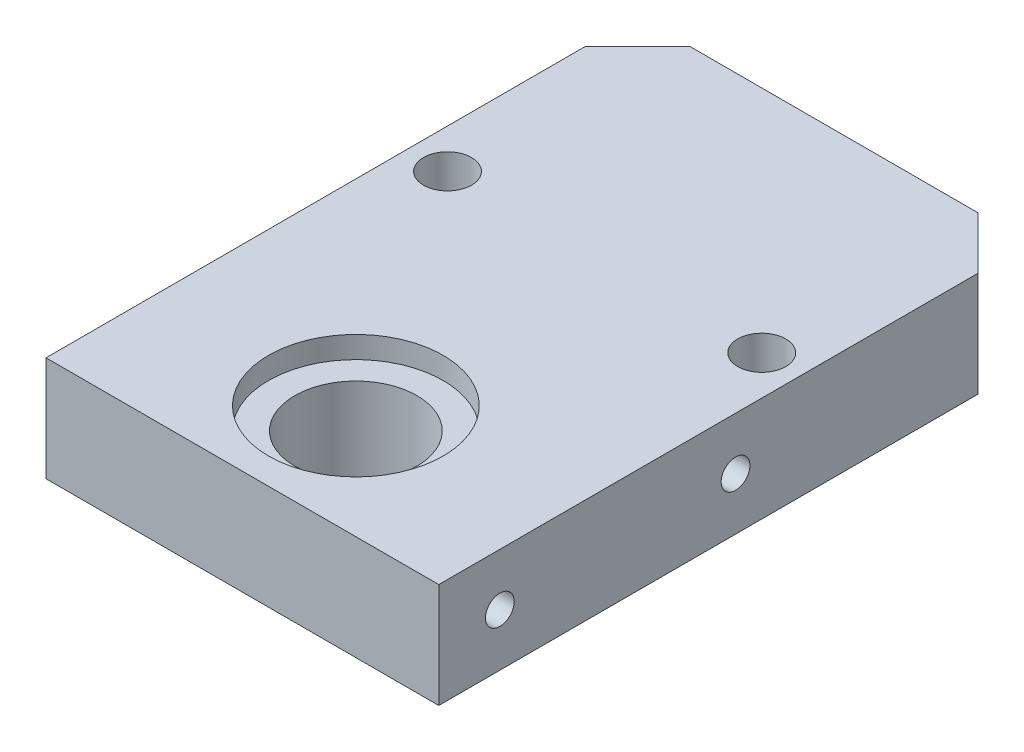
SolidWorks part; units mm, degrees
ref_plane "Front Plane" through (0, 0, 0) normal (0, 0, 1) x (1, 0, 0)
ref_plane "Top Plane" through (0, 0, 0) normal (0, 1, 0) x (1, 0, 0)
ref_plane "Right Plane" through (0, 0, 0) normal (1, 0, 0) x (0, 0, -1)
sketch "Sketch1" plane through (0, 0, 0) normal (0, 1, 0) x (1, 0, 0)
  line L0 (-16.5, 33.8889) -> (-22.5, 27.8889)
  line L1 (-22.5, -33.8889) -> (22.5, -33.8889)
  line L2 (-22.5, -33.8889) -> (-22.5, 27.8889)
  line L3 (-16.5, 33.8889) -> (16.5, 33.8889)
  line L4 (22.5, -33.8889) -> (22.5, 27.8889)
  line L5 (-22.5, -33.8889) -> (22.5, 33.8889) construction
  line L6 (-22.5, 33.8889) -> (22.5, -33.8889) construction
  line L7 (16.5, 33.8889) -> (22.5, 27.8889)
  circle A0 centre (-18, 7.6111) radius 2.75
  circle A1 centre (18, 7.6111) radius 2.75
  circle A2 centre (0, -20.8889) radius 7
  point P0 (0, 0)
  dimension "D8" = 18
  dimension "D10" = 41.5
  dimension "D11" = 41.5
  dimension "D12" = 13
  dimension "D1" = 45
  dimension "D2" = 67.7778
  dimension "D3" = 45
  dimension "D4" = 6
  dimension "D5" = 6
  dimension "D6" = 45
  dimension "D7" = 6
  dimension "D9" = 18
  dimension "D13" = 22.5
extrude "Boss-Extrude1" add sketch "Sketch1" along normal blind 12
hole_wizard "M4 Tapped Hole1" positions "Sketch2" profile "Sketch3" tap size "M4" standard "DIN"
sketch "Sketch2" plane through (-22.5, 0, 0) normal (-1, 0, 0) x (0, 0, 1)
  line L1 (-27.8889, 12) -> (33.8889, 12) construction
  line L2 (33.8889, 12) -> (33.8889, 0) construction
  point P0 (-0.1111, 6)
  point P2 (26.8889, 6)
  dimension "D1" = 6
  dimension "D2" = 6
  dimension "D3" = 7
  dimension "D4" = 34
sketch "Sketch3" plane through (-22.5, 6, -0.1111) normal (0, 1, 0) x (0, 0, 1)
  line L0 (0, 0) -> (0, 14.9914)
  line L1 (0, 14.9914) -> (1.65, 14)
  line L2 (1.65, 14) -> (1.65, 0)
  line L5 (1.65, 0) -> (0, 0)
  line L10 (0, 14.9914) -> (-1.65, 14) construction
  line L11 (0, -6.35) -> (0, 107.95) construction
  dimension "Tap Drill Dia." = 3.3
  dimension "Tap Drill Depth" = 14
  dimension "Drill Angle" = 118
cosmetic thread "Hole Thread1" parameters "D1"=10, "D2"=4
cosmetic thread "Hole Thread2" parameters "D1"=10, "D2"=4
hole_wizard "M4 Tapped Hole2" positions "Sketch4" profile "Sketch5" tap size "M4" standard "DIN"
sketch "Sketch4" plane through (22.5, 0, 0) normal (1, 0, 0) x (0, 0, -1)
  line L0 (-33.8889, 0) -> (27.8889, 0) construction
  line L1 (-33.8889, 12) -> (-33.8889, 0) construction
  point P0 (-26.8889, 6)
  point P2 (0.1111, 6)
  dimension "D1" = 6
  dimension "D2" = 6
  dimension "D3" = 7
  dimension "D4" = 27
sketch "Sketch5" plane through (22.5, 6, 26.8889) normal (0, 1, 0) x (0, 0, -1)
  line L0 (0, 0) -> (0, 14.9914)
  line L1 (0, 14.9914) -> (1.65, 14)
  line L2 (1.65, 14) -> (1.65, 0)
  line L5 (1.65, 0) -> (0, 0)
  line L10 (0, 14.9914) -> (-1.65, 14) construction
  line L11 (0, -6.35) -> (0, 107.95) construction
  dimension "Tap Drill Dia." = 3.3
  dimension "Tap Drill Depth" = 14
  dimension "Drill Angle" = 118
cosmetic thread "Hole Thread3" parameters "D1"=10, "D2"=4
cosmetic thread "Hole Thread4" parameters "D1"=10, "D2"=4
sketch "Sketch6" plane through (0, 12, 0) normal (0, 1, 0) x (1, 0, 0)
  circle A0 centre (0, -20.8889) radius 10
extrude "Cut-Extrude1" cut sketch "Sketch6" against normal blind 2.5
